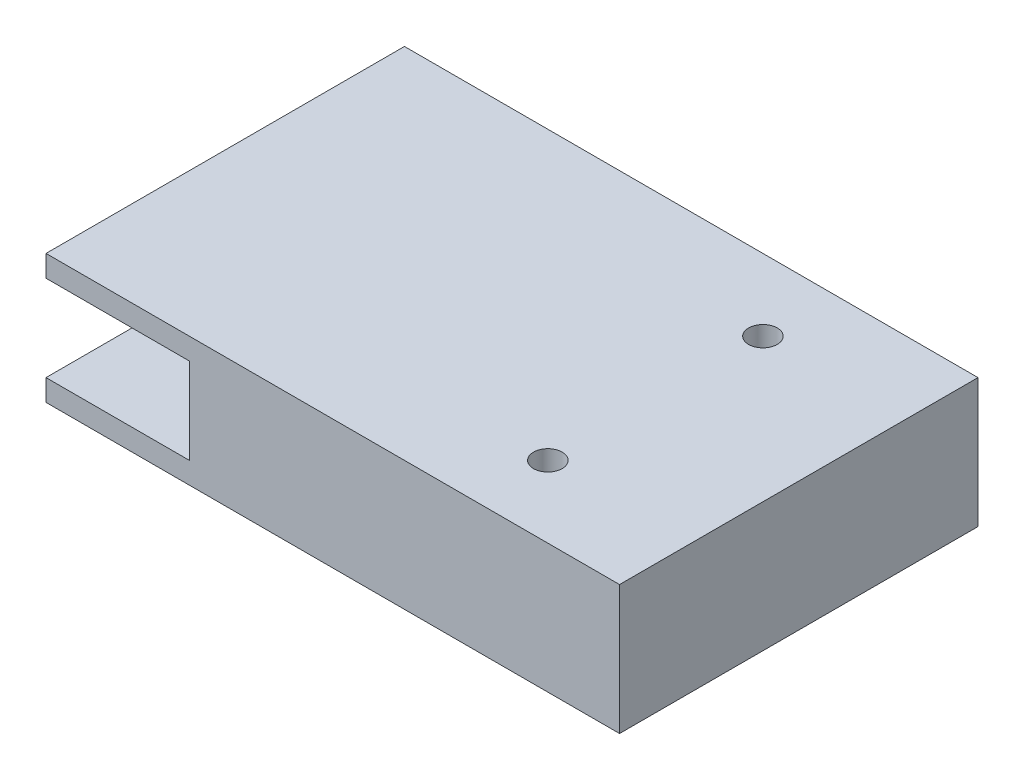
SolidWorks part; units mm, degrees
ref_plane "Front Plane" through (0, 0, 0) normal (0, 0, 1) x (1, 0, 0)
ref_plane "Top Plane" through (0, 0, 0) normal (0, 1, 0) x (1, 0, 0)
ref_plane "Right Plane" through (0, 0, 0) normal (1, 0, 0) x (0, 0, -1)
sketch "Sketch1" plane through (0, 0, 0) normal (0, 1, 0) x (1, 0, 0)
  line L1 (-40, -25) -> (40, -25)
  line L2 (-40, -25) -> (-40, 25)
  line L3 (-40, 25) -> (40, 25)
  line L4 (40, -25) -> (40, 25)
  line L5 (-40, -25) -> (40, 25) construction
  line L6 (-40, 25) -> (40, -25) construction
  point P0 (0, 0)
  dimension "D1" = 50
  dimension "D2" = 80
extrude "Boss-Extrude1" add sketch "Sketch1" along normal blind 3
sketch "Sketch2" plane through (0, 3, 0) normal (0, 1, 0) x (1, 0, 0)
  line L0 (-40, 0) -> (35.7081, 0) construction
  line L1 (-40, 25) -> (-40, -25) construction
  line L2 (-30, 0) -> (-30, 19.5969) construction
  circle A0 centre (-30, 11) radius 2
  circle A1 centre (-30, -11) radius 2
  dimension "D2" = 4
  dimension "D3" = 4
  dimension "D1" = 10
  dimension "D4" = 11
  dimension "D5" = 11
extrude "Boss-Extrude2" add sketch "Sketch2" along normal blind 14
sketch "Sketch3" plane through (0, 3, 0) normal (0, 1, 0) x (1, 0, 0)
  line L0 (-40, -25) -> (40, -25) construction
  line L1 (40, 25) -> (-20, 25)
  line L2 (40, 25) -> (40, -25)
  line L3 (40, -25) -> (-20, -25)
  line L4 (-20, 25) -> (-20, -25)
  dimension "D1" = 60
extrude "Boss-Extrude3" add sketch "Sketch3" along normal blind 12
sketch "Sketch4" plane through (-20, 0, 0) normal (-1, 0, 0) x (0, 0, 1)
  line L0 (0, 3) -> (0, 11) construction
  line L1 (-25, 3) -> (25, 3) construction
  circle A0 centre (0, 11) radius 3
  dimension "D2" = 6
  dimension "D1" = 8
extrude "Cut-Extrude1" cut sketch "Sketch4" against normal blind 10
sketch "Sketch5" plane through (0, 15, 0) normal (0, 1, 0) x (1, 0, 0)
  line L1 (40, 25) -> (-40, 25)
  line L2 (40, 25) -> (40, -25)
  line L3 (40, -25) -> (-40, -25)
  line L4 (-40, 25) -> (-40, -25)
extrude "Boss-Extrude4" add sketch "Sketch5" along normal blind 3
sketch "Sketch6" plane through (0, 18, 0) normal (0, 1, 0) x (1, 0, 0)
  line L0 (40, 0) -> (20, 0) construction
  line L1 (40, -25) -> (40, 25) construction
  line L2 (20, 0) -> (20, 13)
  line L3 (20, 0) -> (20, -13)
  circle A0 centre (20, 15) radius 2
  circle A1 centre (20, -15) radius 2
  dimension "D4" = 4
  dimension "D5" = 4
  dimension "D1" = 20
  dimension "D2" = 15
  dimension "D3" = 15
extrude "Cut-Extrude2" cut sketch "Sketch6" against normal blind 49 contours A1 | A0
sketch "Sketch7" plane through (0, 0, -25) normal (0, 0, -1) x (-1, 0, 0)
  line L0 (-40, 9) -> (20, 9) construction
  line L1 (-40, 18) -> (-40, 0) construction
  line L2 (20, 15) -> (20, 3) construction
  line L4 (15, 11.3094) -> (13, 10.1547)
  line L5 (13, 10.1547) -> (13, 7.8453)
  line L6 (13, 7.8453) -> (15, 6.6906)
  line L7 (15, 6.6906) -> (17, 7.8453)
  line L8 (17, 7.8453) -> (17, 10.1547)
  line L9 (17, 10.1547) -> (15, 11.3094)
  line L10 (5, 11.3094) -> (3, 10.1547)
  line L11 (3, 10.1547) -> (3, 7.8453)
  line L12 (3, 7.8453) -> (5, 6.6906)
  line L13 (5, 6.6906) -> (7, 7.8453)
  line L14 (7, 7.8453) -> (7, 10.1547)
  line L15 (7, 10.1547) -> (5, 11.3094)
  circle A0 centre (15, 9) radius 2 construction
  circle A1 centre (5, 9) radius 2 construction
  dimension "D1" = 4
  dimension "D4" = 4
  dimension "D2" = 5
  dimension "D3" = 10
extrude "Boss-Extrude5" add sketch "Sketch7" along normal blind 3
sketch "Sketch8" plane through (0, 0, -28) normal (0, 0, -1) x (-1, 0, 0)
  circle A0 centre (14.8839, 9) radius 1
  circle A1 centre (5, 9) radius 1
  dimension "D1" = 2
  dimension "D2" = 2
extrude "Boss-Extrude6" add sketch "Sketch8" along normal blind 2
equation "\"1o\"=8"
